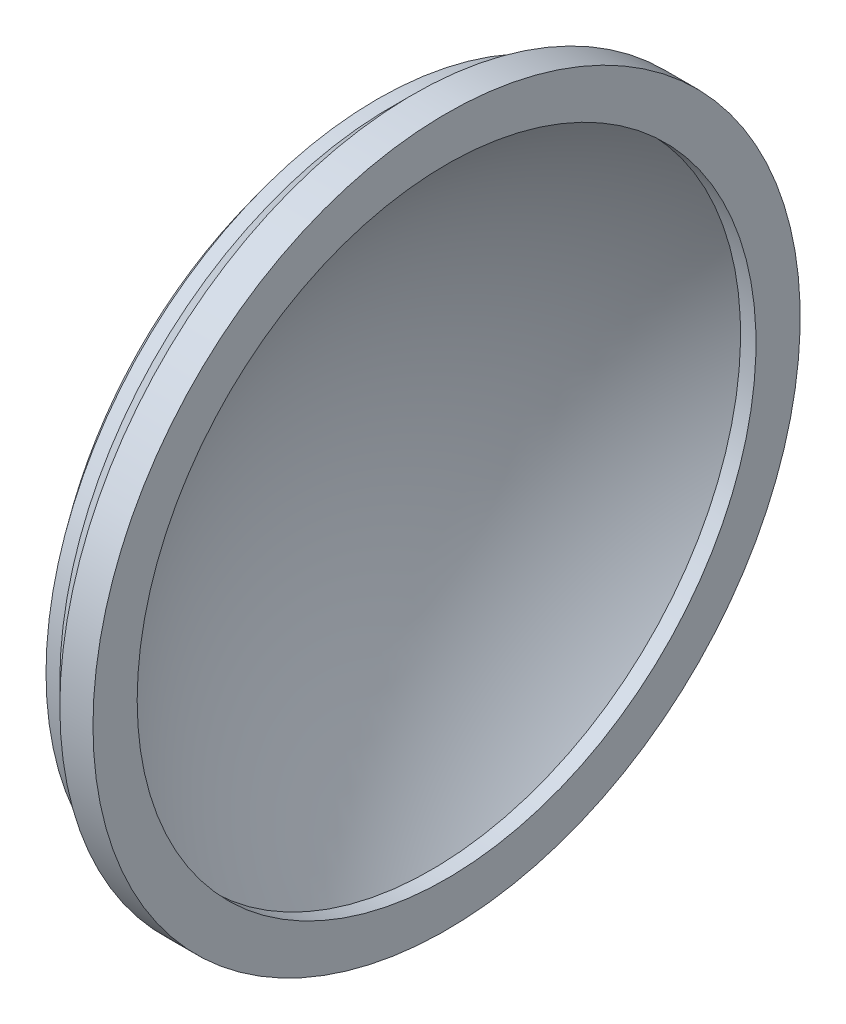
SolidWorks part; units mm, degrees
ref_plane "Front Plane" through (0, 0, 0) normal (0, 0, 1) x (1, 0, 0)
ref_plane "Top Plane" through (0, 0, 0) normal (0, 1, 0) x (1, 0, 0)
ref_plane "Right Plane" through (0, 0, 0) normal (1, 0, 0) x (0, 0, -1)
sketch "Sketch1" plane through (0, 0, 0) normal (0, 0, 1) x (1, 0, 0)
  line L0 (-162.4138, 0) -> (81.499, 0) construction
  line L1 (-28.5, 60) -> (-26, 60)
  line L2 (-26, 60) -> (-22, 64)
  line L3 (-22, 64) -> (-16, 64)
  line L4 (-16, 64) -> (-16, 56)
  line L5 (-16, 56) -> (-18.7907, 56)
  line L6 (-49.8454, 0) -> (-39.8454, 0)
  arc A0 (-28.5, 60) -> (-49.8454, 0) centre (45.1546, 0) ccw
  arc A1 (-18.7907, 56) -> (-39.8454, 0) centre (45.1546, 0) ccw
  dimension "D3" = 95
  dimension "D4" = 85
  dimension "D1" = 16
  dimension "D2" = 64
  dimension "D5" = 2.5
  dimension "D6" = 8
  dimension "D7" = 4
  dimension "D8" = 6
  dimension "D9" = 135
revolve "Revolve1" add sketch "Sketch1" angle 360 about L0
